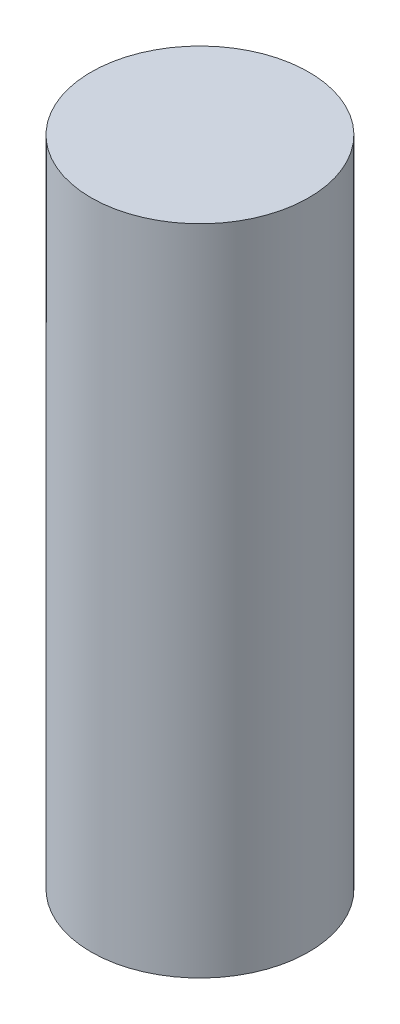
SolidWorks part; units mm, degrees
ref_plane "Front Plane" through (0, 0, 0) normal (0, 0, 1) x (1, 0, 0)
ref_plane "Top Plane" through (0, 0, 0) normal (0, 1, 0) x (1, 0, 0)
ref_plane "Right Plane" through (0, 0, 0) normal (1, 0, 0) x (0, 0, -1)
sketch "Sketch1" plane through (0, 0, 0) normal (0, 1, 0) x (1, 0, 0)
  circle A0 centre (0, 0) radius 5
  dimension "D1" = 10
extrude "Boss-Extrude1" add sketch "Sketch1" along normal mid plane 30
